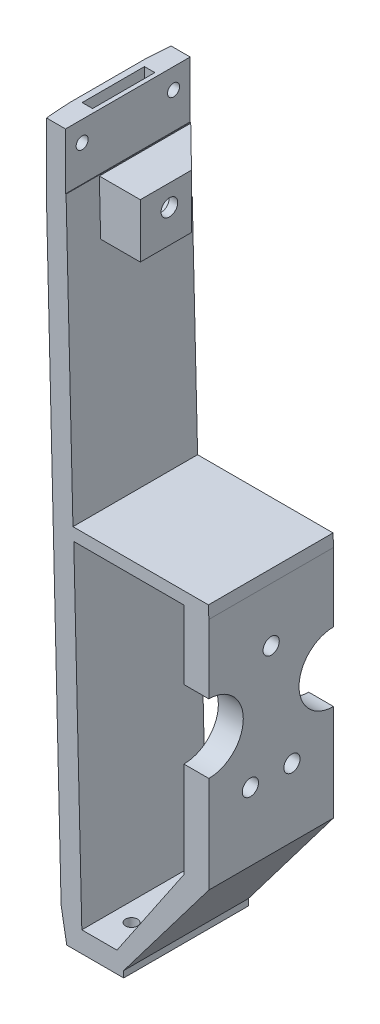
SolidWorks part; units mm, degrees
ref_plane "Front Plane" through (0, 0, 0) normal (0, 0, 1) x (1, 0, 0)
ref_plane "Top Plane" through (0, 0, 0) normal (0, 1, 0) x (1, 0, 0)
ref_plane "Right Plane" through (0, 0, 0) normal (1, 0, 0) x (0, 0, -1)
sketch "Sketch1" plane through (0, 0, 0) normal (0, 0, 1) x (1, 0, 0)
  line L0 (-0.8631, -23.2534) -> (14.1369, -23.2534)
  line L1 (14.1369, -23.2534) -> (14.1369, -21.7046)
  line L2 (14.1369, -21.7046) -> (34.6369, 5.3363)
  line L3 (34.6369, 5.3363) -> (34.6369, 61.7466)
  line L4 (34.6369, 61.7466) -> (28.6369, 61.7466)
  line L5 (28.6369, 61.7466) -> (28.6369, 5.5585)
  line L6 (28.6369, 5.5585) -> (12.5197, -18.2534)
  line L7 (12.5197, -18.2534) -> (-0.8631, -18.2534)
  line L8 (-0.8631, -18.2534) -> (-0.8631, -23.2534)
  dimension "D1" = 6
  dimension "D2" = 15
  dimension "D3" = 5
  dimension "D4" = 35.5
  dimension "D5" = 85
extrude "Extrude1" add sketch "Sketch1" along normal blind 30
sketch "Sketch2" plane through (0, 0, 0) normal (0, 0, 1) x (1, 0, 0)
  line L0 (-0.8631, -18.2534) -> (-4.8631, 146.7466)
  line L1 (-4.8631, 146.7466) -> (-0.0631, 146.7466)
  line L2 (0.1369, 138.4966) -> (1.9252, 64.7291)
  line L3 (1.9252, 64.7291) -> (34.5327, 64.7291)
  line L4 (34.5327, 64.7291) -> (34.6369, 61.7466)
  line L5 (34.6369, 61.7466) -> (28.6369, 61.7466)
  line L6 (28.6369, 61.7466) -> (2.119, 61.7466)
  line L7 (2.119, 61.7466) -> (4.0584, -18.2534)
  line L8 (4.0584, -18.2534) -> (-0.8631, -18.2534)
  line L9 (12.5197, -18.2534) -> (-0.8631, -18.2534) construction
  line L10 (-0.8631, -23.2534) -> (14.1369, -23.2534) construction
  line L11 (-0.0631, 146.7466) -> (0.1369, 146.7466)
  line L12 (0.1369, 146.7466) -> (0.1369, 138.4966)
  dimension "D1" = 170
  dimension "D2" = 4.8
  dimension "D3" = 39.5
  dimension "D4" = 0.2
extrude "Extrude2" add sketch "Sketch2" along normal blind 30
sketch "Sketch4" plane through (34.6369, 0, 0) normal (1, 0, 0) x (0, 0, -1)
  line L0 (0, 5.3363) -> (0, 61.7466) construction
  line L3 (-15, 61.7466) -> (-15, 5.3363) construction
  line L5 (-30, 61.7466) -> (0, 61.7466) construction
  line L6 (-30, 5.3363) -> (0, 5.3363) construction
  circle A0 centre (0, 36.886) radius 8.2888
  circle A1 centre (-30, 36.886) radius 8.2888
extrude "Extrude4" cut sketch "Sketch4" against normal blind 30
sketch "Sketch5" plane through (34.6369, 0, 0) normal (1, 0, 0) x (0, 0, -1)
  line L1 (0, 5.3363) -> (0, 28.5972) construction
  line L2 (-30, 5.3363) -> (-30, 28.5972) construction
  line L3 (-30, 5.3363) -> (0, 5.3363) construction
  circle A0 centre (-20, 21.7466) radius 1.95
  circle A1 centre (-10, 21.7466) radius 1.95
  dimension "D1" = 3.9
  dimension "D2" = 10
  dimension "D3" = 10
  dimension "D4" = 10
  dimension "D5" = 16.4103
extrude "Extrude5" cut sketch "Sketch5" against normal blind 20
sketch "Sketch6" plane through (34.6369, 0, 0) normal (1, 0, 0) x (0, 0, -1)
  line L0 (-30, 61.7466) -> (0, 61.7466) construction
  circle A0 centre (-15, 48.7466) radius 1.95
  point P4 (-15, 61.7466)
  dimension "D1" = 3.9
  dimension "D2" = 13
extrude "Extrude6" cut sketch "Sketch6" against normal blind 20
sketch "Sketch9" plane through (0, -23.2534, 0) normal (0, -1, 0) x (1, 0, 0)
  line L0 (8.5197, 7.5) -> (8.5197, 22.5) construction
  line L1 (-0.8631, 30) -> (-0.8631, 0) construction
  line L2 (-0.8631, 15) -> (14.1369, 15) construction
  line L3 (14.1369, 30) -> (14.1369, 0) construction
  circle A0 centre (8.5197, 7.5) radius 1.45
  circle A1 centre (8.5197, 22.5) radius 1.45
  point P4 (8.5197, 15)
  dimension "D1" = 2.9
  dimension "D2" = 4
  dimension "D3" = 15
extrude "Extrude9" cut sketch "Sketch9" against normal blind 20
sketch "Sketch10" plane through (0, 0, 30) normal (0, 0, 1) x (1, 0, 0)
  line L0 (-4.8293, 145.35) -> (23.0298, 121.9734) construction
  line L1 (23.0298, 121.9734) -> (-4.8293, 119.518) construction
  line L2 (-4.8293, 119.518) -> (-4.8293, 145.35) construction
  line L3 (-4.8631, 146.7466) -> (-0.8631, -18.2534) construction
  dimension "D1" = 50
sketch "Sketch11" plane through (-1.3049, -0.0316, 0) normal (-0.9997, -0.0242, 0) x (0, 0, 1)
  line L0 (30, 145.4243) -> (0, 145.4243) construction
  line L1 (0, 146.8214) -> (0, -18.2271) construction
sketch "Sketch14" plane through (0, 146.7466, 0) normal (0, 1, 0) x (-1, 0, 0)
  line L0 (-0.1369, 0) -> (4.8631, 0) construction
  line L1 (4.4418, 0) -> (4.8631, 0)
  line L2 (4.8631, 0) -> (4.8631, 6.0193)
  spline S0 degree 3 poles (4.4418, 0) (4.5192, 0.8559) (4.7001, 2.8594) (4.8038, 4.8685) (4.8631, 6.0193) knots 0 0 0 0 0.427214 1 1 1 1
  point P2 (0, 0)
extrude "Extrude12" cut sketch "Sketch14" against normal through all
sketch "Sketch16" plane through (0, 0, 30) normal (0, 0, 1) x (1, 0, 0)
  line L0 (1.2495, -23.2534) -> (-1.7396, 17.9017) construction
  line L1 (-0.8631, -23.2534) -> (14.1369, -23.2534) construction
  line L2 (-4.8631, 146.7466) -> (-0.8631, -18.2534) construction
ref_plane "Plane4" through (3.9505, -22.4046, 0) normal (0.1736, -0.9848, 0) x (0.9848, 0.1736, 0)
sketch "Sketch15" plane through (-1.7131, -23.4033, 0) normal (-0.1736, 0.9848, 0) x (-0.9848, -0.1736, 0)
  line L0 (-0.8631, 30) -> (-15.6352, 30) construction
  line L2 (-1.9818, 15) -> (2.0587, 15)
  line L3 (2.0587, 15) -> (2.0587, 30)
  line L4 (2.0587, 30) -> (-2.1309, 30)
  spline S0 degree 3 poles (-2.1309, 30) (-1.6601, 28.7231) (-0.8524, 26.872) (-0.4914, 22.6624) (-1.5046, 16.8425) (-1.7732, 15.8056) (-1.9818, 15) knots 0 0 0 0 0.210481 0.646188 0.725139 1 1 1 1
  dimension "D1" = 15
extrude "Extrude15" cut sketch "Sketch15" along normal blind 10 and the other way blind 4
sketch "Sketch17" plane through (-1.3049, -0.0316, 0) normal (-0.9997, -0.0242, 0) x (0, 0, 1)
  line L2 (30, 146.8214) -> (6.0193, 146.8214) construction
  line L3 (22.5, 136.8214) -> (7.5, 136.8214)
  line L5 (22.5, 136.8214) -> (22.5, 122.3214)
  line L6 (22.5, 122.3214) -> (7.5, 122.3214)
  line L7 (7.5, 136.8214) -> (7.5, 122.3214)
  line L8 (30, 146.8214) -> (30, -15.5586) construction
  point P6 (15, 136.8214)
  dimension "D1" = 10
  dimension "D2" = 14.5
  dimension "D3" = 15
  dimension "D4" = 15
extrude "Extrude17" cut sketch "Sketch17" against normal blind 4
sketch "Sketch18" plane through (-3.3159, 136.7812, 0) normal (0.0242, -0.9997, 0) x (0.9997, 0.0242, 0)
  line L0 (2.6948, 22.5) -> (-1.3052, 22.5) construction
  line L1 (2.6948, 7.5) -> (0.1948, 7.5)
  line L2 (2.6948, 7.5) -> (2.6948, 22.5)
  line L3 (2.6948, 22.5) -> (0.1948, 22.5)
  line L4 (0.1948, 7.5) -> (0.1948, 22.5)
  dimension "D1" = 2.5
extrude "Extrude18" cut sketch "Sketch18" against normal blind 10
sketch "Sketch19" plane through (0.1369, 0, 0) normal (1, 0, 0) x (0, 0, -1)
  line L0 (0, 138.4966) -> (0, 146.7466) construction
  line L1 (0, 132.9966) -> (-22, 132.9966)
  line L2 (0, 132.9966) -> (0, 119.9966)
  line L3 (0, 119.9966) -> (-22, 119.9966)
  line L4 (-22, 132.9966) -> (-22, 119.9966)
  line L5 (-30, 138.4966) -> (0, 138.4966) construction
  dimension "D1" = 22
  dimension "D2" = 13
  dimension "D3" = 5.5
extrude "Extrude19" add sketch "Sketch19" along normal blind 10
sketch "Sketch20" plane through (2.694, 0.0653, 0) normal (-0.9997, -0.0242, 0) x (0, 0, 1)
  line L0 (15, 122.3214) -> (15, 146.7244) construction
  line L1 (7.5, 122.3214) -> (22.5, 122.3214) construction
  line L2 (7.5, 146.7244) -> (22.5, 146.7244) construction
  circle A0 centre (15, 127.6214) radius 4
  dimension "D1" = 8
  dimension "D2" = 9.2
extrude "Extrude20" cut sketch "Sketch20" against normal blind 8.5
sketch "Sketch21" plane through (11.1915, 0.2713, 0) normal (-0.9997, -0.0242, 0) x (0, 0, 1)
  circle A0 centre (15, 127.6214) radius 2
  dimension "D1" = 4
extrude "Extrude21" cut sketch "Sketch21" against normal blind 9
sketch "Sketch22" plane through (0, 132.9966, 0) normal (0, 1, 0) x (-1, 0, 0)
  line L0 (-0.2702, 0) -> (-10.1369, 9.6793)
  line L1 (-10.1369, 0) -> (-10.1369, 22) construction
  line L2 (-10.1369, 9.6793) -> (-10.1369, 0)
  line L3 (-10.1369, 0) -> (-0.2702, 0)
extrude "Extrude22" cut sketch "Sketch22" against normal blind 15
ref_plane "Plane5" through (0, 0, 15) normal (0, 0, 1) x (1, 0, 0)
mirror "Mirror1" about plane through (0, 0, 15) normal (0, 0, 1) of "Extrude12"
mirror "Mirror2" about plane through (0, 0, 15) normal (0, 0, 1) of "Extrude15"
hole_wizard "Ø2.9 (2.9) Diameter Hole1" positions "3DSketch1" profile "Sketch23" hole size "Ø2.9" standard "Ansi Metric"
sketch3d "3DSketch1"
  line L1 (-4.4418, 129.369, 0) -> (-0.9278, -15.5856, 0) construction
  line L2 (-4.8631, 146.7466, 23.9807) -> (-4.8631, 146.7466, 6.0193) construction
  point P0 (-4.7419, 141.7481, 4)
  dimension "D1" = 5
  dimension "D2" = 4
sketch "Sketch23" plane through (-4.7419, 141.7481, 4) normal (0, 0, 1) x (0.0242, -0.9997, 0)
  line L0 (0, 0) -> (0, 10)
  line L1 (0, 10) -> (1.45, 10)
  line L2 (1.45, 10) -> (1.45, 0)
  line L5 (1.45, 0) -> (0, 0)
  line L10 (0, 10) -> (-1.45, 10) construction
  line L11 (0, -6.35) -> (0, 107.95) construction
  dimension "Hole Dia." = 2.9
  dimension "Hole Depth" = 10
  dimension "Drill Angle" = 180
mirror "Mirror3" about plane through (0, 0, 15) normal (0, 0, 1) of "Ø2.9 (2.9) Diameter Hole1"
sketch "Sketch24" plane through (0, 0, 30) normal (0, 0, 1) x (1, 0, 0)
  line L0 (0.1369, 138.4966) -> (0.1369, 133.2315)
  line L1 (0.1369, 133.2315) -> (0.6382, 133.2315)
  line L2 (0.6382, 133.2315) -> (0.1369, 138.4966)
extrude "Extrude23" cut sketch "Sketch24" against normal blind 32
